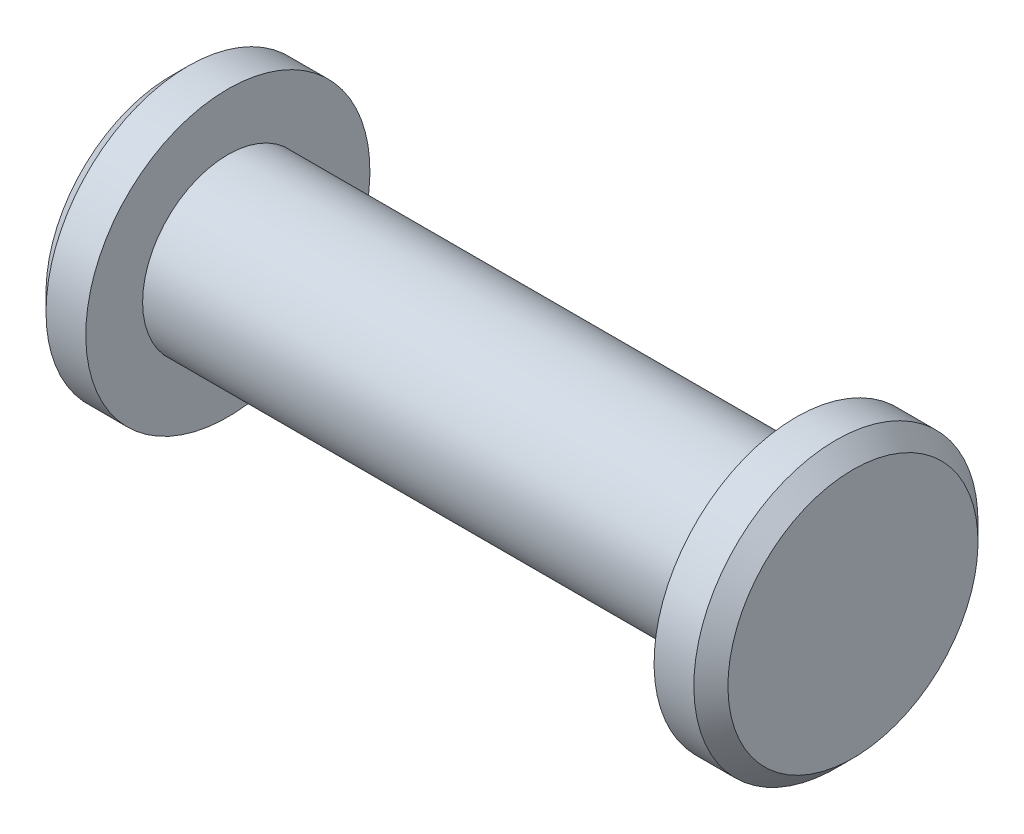
SolidWorks part; units mm, degrees
ref_plane "Front Plane" through (0, 0, 0) normal (0, 0, 1) x (1, 0, 0)
ref_plane "Top Plane" through (0, 0, 0) normal (0, 1, 0) x (1, 0, 0)
ref_plane "Right Plane" through (0, 0, 0) normal (1, 0, 0) x (0, 0, -1)
sketch "Sketch1" plane through (0, 0, 0) normal (0, 0, 1) x (1, 0, 0)
  line L0 (0, 0) -> (-120, 0)
  line L1 (-120, 0) -> (-120, 25)
  line L2 (-120, 25) -> (-110, 25)
  line L3 (-110, 25) -> (-110, 15)
  line L4 (-110, 15) -> (-10, 15)
  line L5 (-10, 15) -> (-10, 25)
  line L6 (-10, 25) -> (0, 25)
  line L7 (0, 25) -> (0, 0)
  dimension "D1" = 100
  dimension "D2" = 10
  dimension "D3" = 10
  dimension "D4" = 15
  dimension "D5" = 25
revolve "Revolve1" add sketch "Sketch1" angle 360 about L0
chamfer "Chamfer1" distance 3 angle 45 2 edges at (-120, 25, 0) (0, 25, 0)
